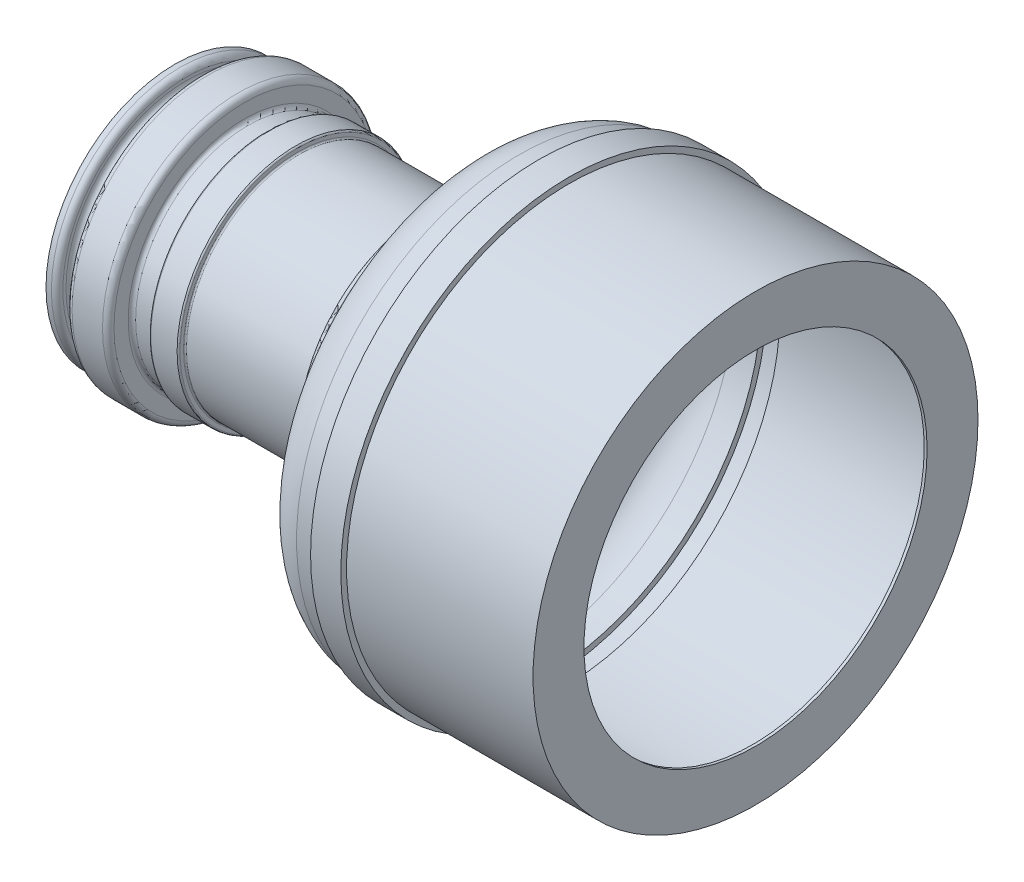
SolidWorks part; units mm, degrees
ref_plane "Front Plane" through (0, 0, 0) normal (0, 0, 1) x (1, 0, 0)
ref_plane "Top Plane" through (0, 0, 0) normal (0, 1, 0) x (1, 0, 0)
ref_plane "Right Plane" through (0, 0, 0) normal (1, 0, 0) x (0, 0, -1)
sketch "Sketch3" plane through (0, 0, 0) normal (0, 1, 0) x (1, 0, 0)
  line L0 (18.96, 1.82) -> (20.82, 1.82)
  line L1 (20.82, 1.82) -> (20.82, 22.2)
  line L2 (20.82, 22.2) -> (14.72, 22.2)
  line L3 (12.72, 20.2) -> (12.72, 17.4)
  line L4 (10.72, 15.4) -> (-31.78, 15.4)
  line L5 (-32.28, 15.9) -> (-32.28, 17.14)
  line L6 (-32.78, 17.64) -> (-41.88, 17.64)
  line L7 (-42.38, 17.14) -> (-42.38, 16.7)
  line L8 (-43.68, 15.4) -> (-49.42, 15.4)
  line L9 (-50.72, 16.7) -> (-50.72, 21.61)
  line L10 (-52.72, 23.61) -> (-63.27, 23.61)
  line L11 (-65.27, 21.61) -> (-65.27, 18.05)
  line L12 (-67.27, 16.05) -> (-68.95, 16.05)
  line L13 (-70.95, 18.05) -> (-70.95, 19.13)
  line L14 (-72.95, 21.13) -> (-74.81, 21.13)
  line L15 (-74.81, 21.13) -> (-74.81, 12.99)
  line L16 (-74.31, 12.49) -> (-61.67, 12.49)
  line L17 (-61.17, 12.99) -> (-61.17, 21.13)
  line L18 (-60.67, 21.63) -> (-55.71, 21.63)
  line L19 (-55.21, 21.13) -> (-55.21, 13.44)
  line L20 (-85.2399, 13.44) -> (-25.1801, 13.44) construction
  line L21 (-68.95, -23.61) -> (61.6549, -23.61) construction
  arc A0 (14.72, 22.2) -> (12.72, 20.2) centre (14.72, 20.2) ccw
  arc A1 (12.72, 17.4) -> (10.72, 15.4) centre (10.72, 17.4) cw
  arc A2 (-41.88, 17.64) -> (-42.38, 17.14) centre (-41.88, 17.14) ccw
  arc A3 (-32.28, 17.14) -> (-32.78, 17.64) centre (-32.78, 17.14) ccw
  arc A4 (-31.78, 15.4) -> (-32.28, 15.9) centre (-31.78, 15.9) cw
  arc A5 (-49.42, 15.4) -> (-50.72, 16.7) centre (-49.42, 16.7) cw
  arc A6 (-42.38, 16.7) -> (-43.68, 15.4) centre (-43.68, 16.7) cw
  arc A7 (-50.72, 21.61) -> (-52.72, 23.61) centre (-52.72, 21.61) ccw
  arc A8 (-63.27, 23.61) -> (-65.27, 21.61) centre (-63.27, 21.61) ccw
  arc A9 (-70.95, 19.13) -> (-72.95, 21.13) centre (-72.95, 19.13) ccw
  arc A10 (-68.95, 16.05) -> (-70.95, 18.05) centre (-68.95, 18.05) cw
  arc A11 (-65.27, 18.05) -> (-67.27, 16.05) centre (-67.27, 18.05) cw
  arc A12 (-55.71, 21.63) -> (-55.21, 21.13) centre (-55.71, 21.13) cw
  arc A13 (-61.17, 21.13) -> (-60.67, 21.63) centre (-60.67, 21.13) cw
  arc A14 (-61.67, 12.49) -> (-61.17, 12.99) centre (-61.67, 12.99) ccw
  arc A15 (-74.81, 12.99) -> (-74.31, 12.49) centre (-74.31, 12.99) ccw
  spline S0 degree 3 poles (18.96, 1.82) (0.2192, 6.529) (-36.5933, 13.44) (-55.21, 13.44) knots 0 0 0 0 1 1 1 1
  point P26 (12.72, 22.2)
  point P29 (12.72, 15.4)
  point P32 (-42.38, 17.64)
  point P35 (-32.28, 17.64)
  point P38 (-32.28, 15.4)
  point P41 (-50.72, 15.4)
  point P44 (-42.38, 15.4)
  point P47 (-50.72, 23.61)
  point P50 (-65.27, 23.61)
  point P53 (-70.95, 21.13)
  point P56 (-70.95, 16.05)
  point P59 (-65.27, 16.05)
  point P62 (-55.21, 21.63)
  point P65 (-61.17, 21.63)
  point P68 (-61.17, 12.49)
  point P71 (-74.81, 12.49)
  dimension "D24" = 2
  dimension "D25" = 0.5
  dimension "D26" = 1.3
  dimension "D27" = 2
  dimension "D28" = 2
  dimension "D29" = 2
  dimension "D30" = 0.5
  dimension "D31" = 55.85
  dimension "D32" = 57.97
  dimension "D1" = 20.38
  dimension "D2" = 1.86
  dimension "D3" = 18.96
  dimension "D4" = 1.82
  dimension "D5" = 18.96
  dimension "D6" = 8.1
  dimension "D7" = 6.8
  dimension "D8" = 45
  dimension "D9" = 2.24
  dimension "D10" = 10.1
  dimension "D11" = 8.21
  dimension "D12" = 8.34
  dimension "D13" = 2.24
  dimension "D14" = 14.55
  dimension "D15" = 5.96
  dimension "D16" = 8.19
  dimension "D17" = 9.14
  dimension "D18" = 5.68
  dimension "D19" = 7.56
  dimension "D20" = 3.86
  dimension "D21" = 8.64
  dimension "D22" = 13.64
  dimension "D23" = 5.08
  dimension "D33" = 130.6049
  dimension "D34" = 23.61
revolve "Revolve1" add sketch "Sketch3" angle 245 about L21
ref_plane "Plane3" through (18.96, 23.0474, 34.3572) normal (0, -0.4226, 0.9063) x (-1, 0, 0)
sketch "Sketch8" plane through (-74.81, 0, 0) normal (-1, 0, 0) x (0, 0, 1)
  circle A0 centre (23.61, 0) radius 25.43 construction
ref_plane "Plane4" through (0, 0, 23.61) normal (0, 0, 1) x (1, 0, 0)
sketch "Sketch11" plane through (0, 0, 0) normal (0, 1, 0) x (1, 0, 0)
  line L0 (20.8197, 1.82) -> (17.8197, 1.82)
  line L1 (17.8197, 1.82) -> (16.1626, 5.0722)
  line L2 (16.1626, 5.0722) -> (16.1626, 23.3022)
  line L3 (16.1626, 23.3022) -> (21.7926, 23.3022)
  line L4 (24.2926, 25.8022) -> (24.2926, 31.1722)
  line L5 (25.7926, 32.6722) -> (28.2926, 32.6722)
  line L6 (37.3137, 41.1422) -> (37.7926, 41.1422)
  line L7 (37.7926, 41.1422) -> (37.7926, 38.2422)
  line L8 (29.9212, 32.6722) -> (26.3028, 32.6722) construction
  line L9 (-14.6752, -22.9373) -> (46.9664, -22.9373) construction
  arc A0 (21.7926, 23.3022) -> (24.2926, 25.8022) centre (21.7926, 25.8022) ccw
  arc A1 (24.2926, 31.1722) -> (25.7926, 32.6722) centre (25.7926, 31.1722) cw
  arc A2 (37.3137, 41.1422) -> (35.9553, 40.2785) centre (37.3137, 39.6422) ccw
  spline S0 degree 3 poles (28.2926, 32.6722) (30.5259, 32.6722) (32.7652, 36.8953) (35.2949, 38.8689) (35.9553, 40.2785) knots 0 0 0 0 0.572842 0.924459 0.924459 0.924459 0.924459
  spline S1 degree 3 poles (37.7926, 38.2422) (31.6131, 30.9129) (28.4965, 23.3559) (21.6193, 7.9178) (20.8197, 1.82) knots 0 0 0 0 0.472364 1 1 1 1
revolve "Revolve2" add sketch "Sketch11" angle 245 about L21
sketch "Sketch12" plane through (0, 0, 0) normal (0, 1, 0) x (1, 0, 0)
  line L0 (31.7574, 30.0357) -> (31.7574, 41.5357)
  line L1 (44.7574, 51.6357) -> (53.5574, 51.6357)
  line L2 (53.5574, 51.6357) -> (53.5574, 53.6357)
  line L3 (53.5574, 53.6357) -> (60.0574, 53.6357)
  line L4 (60.0574, 53.6357) -> (60.0574, 51.6357)
  line L5 (60.0574, 51.6357) -> (125.8074, 51.6357)
  line L6 (125.8074, 51.6357) -> (125.8074, 35.9657)
  line L7 (125.8074, 35.9657) -> (126.8074, 35.9657)
  line L8 (29.7574, 30.0357) -> (29.7574, 41.8575)
  line L9 (44.6802, 53.6357) -> (51.5574, 53.6357)
  line L10 (51.5574, 53.6357) -> (51.5574, 55.6357)
  line L11 (51.5574, 55.6357) -> (62.0574, 55.6357)
  line L12 (62.0574, 55.6357) -> (62.0574, 53.6357)
  line L13 (62.0574, 53.6357) -> (126.8074, 53.6357)
  line L14 (126.8074, 35.9657) -> (126.8074, 53.6357)
  line L15 (62.0574, -23.7818) -> (-69.7086, -23.7818) construction
  line L16 (29.7574, 30.0357) -> (31.7574, 30.0357)
  line L18 (24.2926, 28.4872) -> (24.2926, 41.2601) construction
  line L19 (24.2926, 31.1722) -> (24.2926, 25.8022) construction
  arc A0 (31.7574, 41.5357) -> (44.7574, 51.6357) centre (45.9508, 36.6833) cw
  arc A1 (29.7574, 41.8575) -> (44.6802, 53.6357) centre (45.9508, 36.6833) cw
  dimension "D1" = 64.75
revolve "Revolve3" add sketch "Sketch12" angle 245 about L21
sketch "Sketch29" plane through (126.8074, 0, 0) normal (1, 0, 0) x (0, 0, -1)
  line L0 (-23.61, 0) -> (-55.62, -50.2457) construction
  arc A0 (-48.7878, 53.9939) -> (35.9657, 0) centre (-23.61, 0) ccw construction
sketch "Sketch34" plane through (0, -9.0432, 19.3931) normal (0, 0.4226, -0.9063) x (-1, 0, 0)
  line L44 (-31.7574, 63.6387) -> (-31.7574, 63.6237)
  line L45 (-31.7574, 63.6237) -> (-31.7483, 63.6237)
  line L46 (-20.82, 35.4106) -> (-20.82, 35.408)
  line L47 (-20.82, 35.408) -> (-17.8197, 35.408)
  line L48 (-17.8197, 35.408) -> (-17.6543, 35.7325)
  line L49 (55.21, 47.028) -> (55.21, 54.718)
  line L50 (55.71, 55.218) -> (60.67, 55.218)
  line L51 (61.17, 54.718) -> (61.17, 46.578)
  line L52 (61.67, 46.078) -> (74.31, 46.078)
  line L53 (74.81, 46.578) -> (74.81, 54.718)
  line L54 (74.81, 54.718) -> (72.95, 54.718)
  line L55 (70.95, 52.718) -> (70.95, 51.638)
  line L56 (68.95, 49.638) -> (67.27, 49.638)
  line L57 (65.27, 51.638) -> (65.27, 55.198)
  line L58 (63.27, 57.198) -> (52.72, 57.198)
  line L59 (50.72, 55.198) -> (50.72, 50.288)
  line L60 (49.42, 48.988) -> (43.68, 48.988)
  line L61 (42.38, 50.288) -> (42.38, 50.728)
  line L62 (41.88, 51.228) -> (32.78, 51.228)
  line L63 (32.28, 50.728) -> (32.28, 49.488)
  line L64 (31.78, 48.988) -> (-10.72, 48.988)
  line L65 (-12.72, 50.988) -> (-12.72, 53.788)
  line L66 (-14.72, 55.788) -> (-16.1626, 55.788)
  line L67 (-16.1626, 55.788) -> (-16.1626, 56.8902)
  line L68 (-16.1626, 56.8902) -> (-21.7926, 56.8902)
  line L69 (-24.2926, 59.3902) -> (-24.2926, 64.7602)
  line L70 (-25.7926, 66.2602) -> (-28.2926, 66.2602)
  line L71 (-29.7574, 66.6585) -> (-29.7574, 75.4455)
  line L72 (-44.6802, 87.2237) -> (-51.5574, 87.2237)
  line L73 (-51.5574, 87.2237) -> (-51.5574, 89.2237)
  line L74 (-51.5574, 89.2237) -> (-62.0574, 89.2237)
  line L75 (-62.0574, 89.2237) -> (-62.0574, 87.2237)
  line L76 (-62.0574, 87.2237) -> (-126.8074, 87.2237)
  line L77 (-126.8074, 87.2237) -> (-126.8074, 69.5537)
  line L78 (-126.8074, 69.5537) -> (-125.8074, 69.5537)
  line L79 (-125.8074, 69.5537) -> (-125.8074, 85.2237)
  line L80 (-125.8074, 85.2237) -> (-60.0574, 85.2237)
  line L81 (-60.0574, 85.2237) -> (-60.0574, 87.2237)
  line L82 (-60.0574, 87.2237) -> (-53.5574, 87.2237)
  line L83 (-53.5574, 87.2237) -> (-53.5574, 85.2237)
  line L84 (-53.5574, 85.2237) -> (-44.7574, 85.2237)
  line L85 (-31.7574, 75.1237) -> (-31.7574, 68.52)
  line L86 (-37.3137, 74.7302) -> (-37.7926, 74.7302)
  line L87 (-37.7926, 74.7302) -> (-37.7926, 71.8302)
  line L88 (-31.7574, 63.6387) -> (-31.7574, 63.6237)
  line L89 (-31.7574, 63.6237) -> (-31.7483, 63.6237)
  line L90 (-20.82, 35.4106) -> (-20.82, 35.408)
  line L91 (-20.82, 35.408) -> (-17.8197, 35.408)
  line L92 (-17.8197, 35.408) -> (-17.6543, 35.7325)
  line L93 (55.21, 47.028) -> (55.21, 54.718)
  line L94 (55.71, 55.218) -> (60.67, 55.218)
  line L95 (61.17, 54.718) -> (61.17, 46.578)
  line L96 (61.67, 46.078) -> (74.31, 46.078)
  line L97 (74.81, 46.578) -> (74.81, 54.718)
  line L98 (74.81, 54.718) -> (72.95, 54.718)
  line L99 (70.95, 52.718) -> (70.95, 51.638)
  line L100 (68.95, 49.638) -> (67.27, 49.638)
  line L101 (65.27, 51.638) -> (65.27, 55.198)
  line L102 (63.27, 57.198) -> (52.72, 57.198)
  line L103 (50.72, 55.198) -> (50.72, 50.288)
  line L104 (49.42, 48.988) -> (43.68, 48.988)
  line L105 (42.38, 50.288) -> (42.38, 50.728)
  line L106 (41.88, 51.228) -> (32.78, 51.228)
  line L107 (32.28, 50.728) -> (32.28, 49.488)
  line L108 (31.78, 48.988) -> (-10.72, 48.988)
  line L109 (-12.72, 50.988) -> (-12.72, 53.788)
  line L110 (-14.72, 55.788) -> (-16.1626, 55.788)
  line L111 (-16.1626, 55.788) -> (-16.1626, 56.8902)
  line L112 (-16.1626, 56.8902) -> (-21.7926, 56.8902)
  line L113 (-24.2926, 59.3902) -> (-24.2926, 64.7602)
  line L114 (-25.7926, 66.2602) -> (-28.2926, 66.2602)
  line L115 (-29.7574, 66.6585) -> (-29.7574, 75.4455)
  line L116 (-44.6802, 87.2237) -> (-51.5574, 87.2237)
  line L117 (-51.5574, 87.2237) -> (-51.5574, 89.2237)
  line L118 (-51.5574, 89.2237) -> (-62.0574, 89.2237)
  line L119 (-62.0574, 89.2237) -> (-62.0574, 87.2237)
  line L120 (-62.0574, 87.2237) -> (-126.8074, 87.2237)
  line L121 (-126.8074, 87.2237) -> (-126.8074, 69.5537)
  line L122 (-126.8074, 69.5537) -> (-125.8074, 69.5537)
  line L123 (-125.8074, 69.5537) -> (-125.8074, 85.2237)
  line L124 (-125.8074, 85.2237) -> (-60.0574, 85.2237)
  line L125 (-60.0574, 85.2237) -> (-60.0574, 87.2237)
  line L126 (-60.0574, 87.2237) -> (-53.5574, 87.2237)
  line L127 (-53.5574, 87.2237) -> (-53.5574, 85.2237)
  line L128 (-53.5574, 85.2237) -> (-44.7574, 85.2237)
  line L129 (-31.7574, 75.1237) -> (-31.7574, 68.52)
  line L130 (-37.3137, 74.7302) -> (-37.7926, 74.7302)
  line L131 (-37.7926, 74.7302) -> (-37.7926, 71.8302)
  arc A21 (55.71, 55.218) -> (55.21, 54.718) centre (55.71, 54.718) ccw
  arc A22 (61.17, 54.718) -> (60.67, 55.218) centre (60.67, 54.718) ccw
  arc A23 (61.17, 46.578) -> (61.67, 46.078) centre (61.67, 46.578) ccw
  arc A24 (74.31, 46.078) -> (74.81, 46.578) centre (74.31, 46.578) ccw
  arc A25 (72.95, 54.718) -> (70.95, 52.718) centre (72.95, 52.718) ccw
  arc A26 (68.95, 49.638) -> (70.95, 51.638) centre (68.95, 51.638) ccw
  arc A27 (65.27, 51.638) -> (67.27, 49.638) centre (67.27, 51.638) ccw
  arc A28 (65.27, 55.198) -> (63.27, 57.198) centre (63.27, 55.198) ccw
  arc A29 (52.72, 57.198) -> (50.72, 55.198) centre (52.72, 55.198) ccw
  arc A30 (49.42, 48.988) -> (50.72, 50.288) centre (49.42, 50.288) ccw
  arc A31 (42.38, 50.288) -> (43.68, 48.988) centre (43.68, 50.288) ccw
  arc A32 (42.38, 50.728) -> (41.88, 51.228) centre (41.88, 50.728) ccw
  arc A33 (32.78, 51.228) -> (32.28, 50.728) centre (32.78, 50.728) ccw
  arc A34 (31.78, 48.988) -> (32.28, 49.488) centre (31.78, 49.488) ccw
  arc A35 (-12.72, 50.988) -> (-10.72, 48.988) centre (-10.72, 50.988) ccw
  arc A36 (-12.72, 53.788) -> (-14.72, 55.788) centre (-14.72, 53.788) ccw
  arc A37 (-24.2926, 59.3902) -> (-21.7926, 56.8902) centre (-21.7926, 59.3902) ccw
  arc A38 (-24.2926, 64.7602) -> (-25.7926, 66.2602) centre (-25.7926, 64.7602) ccw
  arc A39 (-29.7574, 75.4455) -> (-44.6802, 87.2237) centre (-45.9508, 70.2713) ccw
  arc A40 (-31.7574, 75.1237) -> (-44.7574, 85.2237) centre (-45.9508, 70.2713) ccw
  arc A41 (-35.9553, 73.8666) -> (-37.3137, 74.7302) centre (-37.3137, 73.2302) ccw
  arc A42 (55.71, 55.218) -> (55.21, 54.718) centre (55.71, 54.718) ccw
  arc A43 (61.17, 54.718) -> (60.67, 55.218) centre (60.67, 54.718) ccw
  arc A44 (61.17, 46.578) -> (61.67, 46.078) centre (61.67, 46.578) ccw
  arc A45 (74.31, 46.078) -> (74.81, 46.578) centre (74.31, 46.578) ccw
  arc A46 (72.95, 54.718) -> (70.95, 52.718) centre (72.95, 52.718) ccw
  arc A47 (68.95, 49.638) -> (70.95, 51.638) centre (68.95, 51.638) ccw
  arc A48 (65.27, 51.638) -> (67.27, 49.638) centre (67.27, 51.638) ccw
  arc A49 (65.27, 55.198) -> (63.27, 57.198) centre (63.27, 55.198) ccw
  arc A50 (52.72, 57.198) -> (50.72, 55.198) centre (52.72, 55.198) ccw
  arc A51 (49.42, 48.988) -> (50.72, 50.288) centre (49.42, 50.288) ccw
  arc A52 (42.38, 50.288) -> (43.68, 48.988) centre (43.68, 50.288) ccw
  arc A53 (42.38, 50.728) -> (41.88, 51.228) centre (41.88, 50.728) ccw
  arc A54 (32.78, 51.228) -> (32.28, 50.728) centre (32.78, 50.728) ccw
  arc A55 (31.78, 48.988) -> (32.28, 49.488) centre (31.78, 49.488) ccw
  arc A56 (-12.72, 50.988) -> (-10.72, 48.988) centre (-10.72, 50.988) ccw
  arc A57 (-12.72, 53.788) -> (-14.72, 55.788) centre (-14.72, 53.788) ccw
  arc A58 (-24.2926, 59.3902) -> (-21.7926, 56.8902) centre (-21.7926, 59.3902) ccw
  arc A59 (-24.2926, 64.7602) -> (-25.7926, 66.2602) centre (-25.7926, 64.7602) ccw
  arc A60 (-29.7574, 75.4455) -> (-44.6802, 87.2237) centre (-45.9508, 70.2713) ccw
  arc A61 (-31.7574, 75.1237) -> (-44.7574, 85.2237) centre (-45.9508, 70.2713) ccw
  arc A62 (-35.9553, 73.8666) -> (-37.3137, 74.7302) centre (-37.3137, 73.2302) ccw
  spline S5 degree 3 poles (-2209.7861, 2141.1367) (2033.7575, -1927.2664) (-2039.6384, 2088.2824) (1991.8107, -2150.0283) knots -2.249327 -2.249327 -2.249327 -2.249327 4.533539 4.533539 4.533539 4.533539 only from (-37.7926, 71.8302) to (-31.7574, 63.6387)
  spline S6 degree 3 poles (-2202.5185, 2134.1691) (-15.9672, 37.9267) (-82.5057, 169.1322) (93.8331, -208.6677) (-2188.2325, 2107.3174) knots -3.245843 -3.245843 -3.245843 -3.245843 0.256976 4.790698 4.790698 4.790698 4.790698 only from (-31.7483, 63.6237) to (-20.82, 35.4106)
  spline S7 degree 3 poles (2916.0727, 661.3877) (-3354.3528, -747.546) (3363.5032, 920.3199) (-2810.3877, -837.9) knots -4.009162 -4.009162 -4.009162 -4.009162 4.926943 4.926943 4.926943 4.926943 only from (-17.6543, 35.7325) to (55.21, 47.028)
  spline S8 degree 3 poles (847.3957, 2935.1279) (-834.9657, -2878.1691) (749.7777, 3024.0511) (-850.6755, -2818.4693) knots -4.184952 -4.184952 -4.184952 -4.184952 6.635844 6.635844 6.635844 6.635844 only from (-28.2926, 66.2602) to (-29.7574, 66.6585)
  spline S9 degree 3 poles (847.6841, 2936.1246) (-14.8382, -44.2937) (-22.6275, 143.6415) (-68.9057, 33.4755) (946.3623, 2908.2591) knots -5.335897 -5.335897 -5.335897 -5.335897 0.210537 5.306001 5.306001 5.306001 5.306001 only from (-31.7574, 68.52) to (-35.9553, 73.8666)
  spline S10 degree 3 poles (-37.7926, 71.8302) (-34.98, 68.4943) (-33.1426, 65.9372) (-31.7574, 63.6387) knots 0.785004 0.785004 0.785004 0.785004 1 1 1 1
  spline S11 degree 3 poles (-31.7483, 63.6237) (-30.0955, 60.8785) (-27.015, 53.6183) (-21.6204, 41.5081) (-20.82, 35.4106) knots 0.000075 0.000075 0.000075 0.000075 0.256976 0.784537 0.784537 0.784537 0.784537
  spline S12 degree 3 poles (-17.6543, 35.7325) (1.445, 40.4277) (37.0165, 47.028) (55.21, 47.028) knots 0 0 0 0 0.977268 0.977268 0.977268 0.977268
  spline S13 degree 3 poles (-28.2926, 66.2602) (-28.8245, 66.2602) (-29.3085, 66.4086) (-29.7574, 66.6585) knots 0.788022 0.788022 0.788022 0.788022 0.924459 0.924459 0.924459 0.924459
  spline S14 degree 3 poles (-31.7574, 68.52) (-32.3257, 69.2249) (-33.7566, 71.2568) (-35.2949, 72.4569) (-35.9553, 73.8666) knots 0 0 0 0 0.210537 0.562154 0.562154 0.562154 0.562154
  dimension "D1" = 0
revolve "Revolve4" add sketch "Sketch34" angle 115 about L21
sketch "Sketch36" plane through (62.0574, 0, 0) normal (1, 0, 0) x (0, 0, -1)
  circle A0 centre (-23.61, 0) radius 79.2457
  dimension "D1" = 158.4914
scale "Scale1" scale about origin uniform scaling yes scale factor 10
sketch "Sketch38" plane through (620.5737, 0, 0) normal (1, 0, 0) x (0, 0, -1)
  circle A0 centre (-236.1, 0) radius 792.4572
scale "Scale2" scale about origin uniform scaling yes scale factor 0.75
